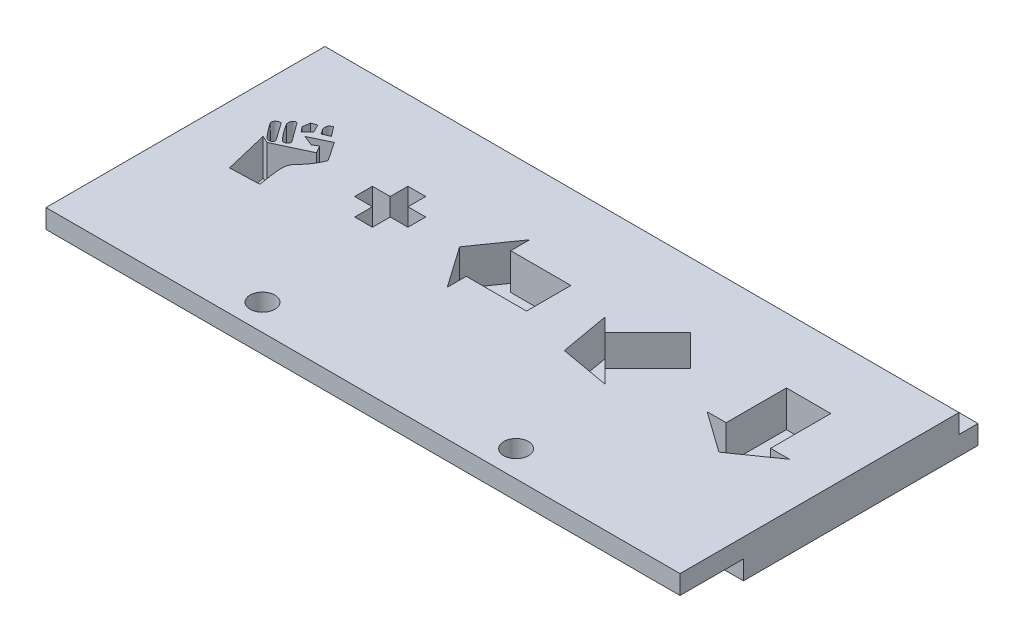
SolidWorks part; units mm, degrees
ref_plane "Front Plane" through (0, 0, 0) normal (0, 0, 1) x (1, 0, 0)
ref_plane "Top Plane" through (0, 0, 0) normal (0, 1, 0) x (1, 0, 0)
ref_plane "Right Plane" through (0, 0, 0) normal (1, 0, 0) x (0, 0, -1)
sketch "Sketch1" plane through (0, 0, 0) normal (0, 1, 0) x (1, 0, 0)
  line L1 (0, 0) -> (100, 0)
  line L2 (0, 0) -> (0, 50)
  line L3 (0, 50) -> (100, 50)
  line L4 (100, 0) -> (100, 50)
  dimension "D1" = 50
  dimension "D2" = 100
extrude "Boss-Extrude1" add sketch "Sketch1" along normal blind 6
sketch "Sketch2" plane through (100, 0, 0) normal (1, 0, 0) x (0, 0, -1)
  line L1 (0, 0) -> (10, 0)
  line L2 (0, 0) -> (0, 3)
  line L3 (0, 3) -> (10, 3)
  line L4 (10, 0) -> (10, 3)
  dimension "D1" = 10
  dimension "D2" = 3
extrude "Cut-Extrude1" cut sketch "Sketch2" against normal through all
sketch "Sketch3" plane through (100, 0, 0) normal (1, 0, 0) x (0, 0, -1)
  line L1 (50, 0) -> (44, 0)
  line L2 (50, 0) -> (50, 34)
  line L3 (50, 34) -> (44, 34)
  line L4 (44, 0) -> (44, 34)
  dimension "D1" = 6
  dimension "D2" = 34
extrude "Boss-Extrude2" add sketch "Sketch3" against normal up to surface (100 mm away) up to face at (0, 3, -20)
sketch "Sketch4" plane through (0, 0, 0) normal (-1, 0, 0) x (0, 0, 1)
  line L1 (-44, 34) -> (-46, 34)
  line L2 (-44, 34) -> (-44, 31)
  line L3 (-44, 31) -> (-46, 31)
  line L4 (-46, 34) -> (-46, 31)
  dimension "D1" = 2
  dimension "D2" = 3
extrude "Cut-Extrude2" cut sketch "Sketch4" against normal through all
sketch "Sketch5" plane through (0, 0, -44) normal (0, 0, -1) x (-1, 0, 0)
  line L0 (-7, 25) -> (-95, 25) construction
  line L1 (-45.0882, 17.5714) -> (-45.4397, 17.4542)
  line L2 (0, 34) -> (-100, 34) construction
  line L5 (-17.0385, 9.6194) -> (-19.4883, 12.0859)
  line L6 (-19.4883, 12.0859) -> (-19.5357, 12.3092)
  line L7 (-19.5357, 12.3092) -> (-19.5273, 14.7589)
  line L8 (-19.5273, 14.7589) -> (-19.4855, 14.904)
  line L9 (-19.4855, 14.904) -> (-16.8962, 17.4542)
  line L10 (-16.8962, 17.4542) -> (-16.5558, 17.5714)
  line L11 (-16.5558, 17.5714) -> (-10.25, 17.5714)
  line L12 (-10.25, 17.5714) -> (-10.2444, 23.8689)
  line L13 (-8.8214, 23.7405) -> (-8.8214, 9.8008)
  line L15 (-9.7478, 9.3767) -> (-16.3744, 9.3571)
  line L16 (-18.1071, 12.5631) -> (-16.154, 10.6071)
  line L17 (-16.154, 10.6071) -> (-10.25, 10.6071)
  line L18 (-10.25, 10.6071) -> (-10.25, 16.3214)
  line L19 (-10.25, 16.3214) -> (-16.1373, 16.3214)
  line L20 (-16.1373, 16.3214) -> (-18.1071, 14.3683)
  line L21 (-18.1071, 14.3683) -> (-18.1071, 12.5631)
  line L23 (-33.8214, 10.1328) -> (-33.8158, 23.88)
  line L25 (-33.1406, 24.3571) -> (-23.5089, 24.3571)
  line L27 (-23.1071, 23.5229) -> (-23.1071, 9.7812)
  line L28 (-23.6094, 9.3571) -> (-33.2355, 9.3795)
  line L29 (-32.3929, 23.1071) -> (-32.3929, 10.6071)
  line L30 (-32.3929, 10.6071) -> (-24.5357, 10.6071)
  line L31 (-24.5357, 10.6071) -> (-24.5357, 23.1071)
  line L32 (-24.5357, 23.1071) -> (-32.3929, 23.1071)
  line L33 (-45.6099, 9.6194) -> (-48.0597, 12.0859)
  line L34 (-48.0597, 12.0859) -> (-48.1071, 12.3092)
  line L35 (-48.1071, 12.3092) -> (-48.0988, 14.7617)
  line L36 (-48.0988, 14.7617) -> (-48.0569, 14.9012)
  line L37 (-48.0569, 14.9012) -> (-45.4397, 17.4542)
  line L39 (-45.0882, 17.5714) -> (-41.6814, 17.5714)
  line L40 (-41.6814, 17.5714) -> (-48.0318, 23.5731)
  line L41 (-46.9911, 24.2595) -> (-40.1161, 17.5714)
  line L42 (-40.1161, 17.5714) -> (-38.8214, 17.5714)
  line L43 (-38.8214, 17.5714) -> (-38.8186, 23.88)
  line L44 (-37.3929, 23.7405) -> (-37.3929, 9.8008)
  line L46 (-38.3192, 9.3767) -> (-44.9459, 9.3571)
  line L47 (-46.6786, 12.5575) -> (-44.7254, 10.6071)
  line L48 (-44.7254, 10.6071) -> (-38.8214, 10.6071)
  line L49 (-38.8214, 10.6071) -> (-38.8214, 16.3214)
  line L50 (-38.8214, 16.3214) -> (-44.7087, 16.3214)
  line L51 (-44.7087, 16.3214) -> (-46.6786, 14.3544)
  line L52 (-46.6786, 14.3544) -> (-46.6786, 12.5575)
  line L54 (-62.3929, 10.1328) -> (-62.3873, 23.88)
  line L56 (-61.7121, 24.3571) -> (-52.0804, 24.3571)
  line L58 (-51.6786, 23.5229) -> (-51.6786, 9.7812)
  line L59 (-52.1808, 9.3571) -> (-61.8069, 9.3795)
  line L60 (-60.9643, 23.1071) -> (-60.9643, 10.6071)
  line L61 (-60.9643, 10.6071) -> (-53.1071, 10.6071)
  line L62 (-53.1071, 10.6071) -> (-53.1071, 23.1071)
  line L63 (-53.1071, 23.1071) -> (-60.9643, 23.1071)
  line L65 (-76.5167, 10.2249) -> (-69.8343, 16.8906)
  line L66 (-69.8343, 16.8906) -> (-76.5084, 23.5647)
  line L67 (-75.4565, 24.2595) -> (-68.6708, 17.5714)
  line L68 (-68.6708, 17.5714) -> (-67.3929, 17.5714)
  line L69 (-67.3929, 17.5714) -> (-67.3901, 23.88)
  line L70 (-65.9643, 23.7405) -> (-65.9643, 9.7896)
  line L71 (-67.3929, 10.1384) -> (-67.3929, 16.3214)
  line L72 (-67.3929, 16.3214) -> (-68.668, 16.3214)
  line L73 (-68.668, 16.3214) -> (-75.49, 9.466)
  line L74 (-81.6786, 10.13) -> (-81.6786, 21.2266)
  line L75 (-81.6786, 21.2266) -> (-83.5703, 23.1071)
  line L76 (-83.5703, 23.1071) -> (-87.5854, 23.1071)
  line L77 (-87.5854, 23.1071) -> (-89.5357, 21.1512)
  line L78 (-89.5357, 21.1512) -> (-89.5357, 9.7701)
  line L79 (-90.9643, 10.1356) -> (-90.8834, 21.7511)
  line L80 (-90.8834, 21.7511) -> (-88.2578, 24.3209)
  line L81 (-88.2578, 24.3209) -> (-87.8728, 24.3571)
  line L82 (-87.8728, 24.3571) -> (-82.9704, 24.3571)
  line L83 (-82.9704, 24.3571) -> (-82.7891, 24.2344)
  line L84 (-82.7891, 24.2344) -> (-80.303, 21.7427)
  line L85 (-80.303, 21.7427) -> (-80.25, 21.4805)
  line L86 (-80.25, 21.4805) -> (-80.25, 9.7812)
  arc A0 (-10.2444, 23.8689) -> (-8.8214, 23.7405) centre (-9.5272, 23.8682) cw
  arc A1 (-23.6094, 9.3571) -> (-23.1071, 9.7812) centre (-23.6082, 9.8652) ccw
  arc A2 (-33.8214, 10.1328) -> (-33.2355, 9.3795) centre (-33.0446, 10.1325) ccw
  arc A3 (-33.8158, 23.88) -> (-33.1406, 24.3571) centre (-33.3095, 23.8798) cw
  arc A4 (-23.1071, 23.5229) -> (-23.5089, 24.3571) centre (-24.1742, 23.5229) ccw
  arc A5 (-9.7478, 9.3767) -> (-8.8214, 9.8008) centre (-9.7514, 10.6083) ccw
  arc A6 (-16.3744, 9.3571) -> (-17.0385, 9.6194) centre (-16.3773, 10.3218) cw
  arc A7 (-38.3192, 9.3767) -> (-37.3929, 9.8008) centre (-38.3228, 10.6083) ccw
  arc A8 (-44.9459, 9.3571) -> (-45.6099, 9.6194) centre (-44.9487, 10.3218) cw
  arc A9 (-38.8186, 23.88) -> (-37.3929, 23.7405) centre (-38.8219, 16.4911) cw
  arc A10 (-46.9911, 24.2595) -> (-48.0318, 23.5731) centre (-47.4361, 23.802) ccw
  arc A11 (-52.1808, 9.3571) -> (-51.6786, 9.7812) centre (-52.1796, 9.8652) ccw
  arc A12 (-61.8069, 9.3795) -> (-62.3929, 10.1328) centre (-61.8055, 9.9851) cw
  arc A13 (-62.3873, 23.88) -> (-61.7121, 24.3571) centre (-61.881, 23.8798) cw
  arc A14 (-51.6786, 23.5229) -> (-52.0804, 24.3571) centre (-52.7456, 23.5229) ccw
  arc A15 (-67.3929, 10.1384) -> (-65.9643, 9.7896) centre (-66.636, 10.1384) ccw
  arc A16 (-76.5167, 10.2249) -> (-75.49, 9.466) centre (-73.495, 13.239) ccw
  arc A17 (-65.9643, 23.7405) -> (-67.3901, 23.88) centre (-66.684, 23.7405) ccw
  arc A18 (-75.4565, 24.2595) -> (-76.5084, 23.5647) centre (-75.9088, 23.8006) ccw
  arc A19 (-80.25, 9.7812) -> (-81.6786, 10.13) centre (-80.25, 12.8814) cw
  arc A20 (-89.5357, 9.7701) -> (-90.9643, 10.1356) centre (-89.5357, 12.7446) cw
  dimension "D1" = 9
extrude "Cut-Extrude3" cut sketch "Sketch5" along normal blind 5.5
sketch "Sketch8" plane through (0, 6, 0) normal (0, 1, 0) x (1, 0, 0)
  line L0 (46.515, 10) -> (46.515, 44) construction
  line L1 (60.1307, 150.748) -> (217.464, 150.748) construction
  line L2 (130, 309) -> (530, 309) construction
  line L3 (101.6667, 132) -> (448.3333, 132) construction
  line L4 (92.1667, 73.5) -> (454.8333, 73.5) construction
  line L12 (92.1667, 73.5) -> (454.8333, 73.5) construction
  line L30 (100, 44) -> (0, 44) construction
  line L64 (50, 44) -> (50, 5.4119) construction
  line L65 (7.0116, 30.0772) -> (8.9551, 27.3326)
  line L66 (8.4762, 31.0134) -> (10.3204, 28.5061)
  line L67 (10.8168, 31.4007) -> (10.155, 32.7243)
  line L68 (9.8241, 30.4081) -> (10.8168, 31.4007)
  line L69 (9.1624, 31.2353) -> (9.8241, 30.4081)
  line L70 (9.3278, 32.3934) -> (9.1624, 31.2353)
  line L71 (10.155, 32.7243) -> (9.3278, 32.3934)
  line L72 (12.8021, 32.2279) -> (11.644, 33.7169)
  line L73 (11.644, 31.7316) -> (12.8021, 32.2279)
  line L74 (11.644, 31.7316) -> (11.0923, 32.5507)
  line L75 (13.193, 29.9735) -> (13.8548, 28.8154)
  line L76 (13.8548, 28.8154) -> (8.5607, 26.3338)
  line L77 (8.5607, 26.3338) -> (7.4026, 26.8301)
  line L78 (7.4026, 26.8301) -> (9.057, 19.8816)
  line L79 (9.057, 19.8816) -> (13.6893, 20.0471)
  line L80 (15.8401, 28.65) -> (13.8548, 31.6279)
  line L81 (13.8548, 31.6279) -> (10.7114, 30.139)
  line L82 (10.7114, 30.139) -> (12.3658, 29.4772)
  line L83 (13.193, 29.9735) -> (12.3658, 29.4772)
  line L84 (31.2401, 25.85) -> (31.2401, 28.65)
  line L85 (28.4401, 25.85) -> (31.2401, 25.85)
  line L86 (28.4401, 23.05) -> (28.4401, 25.85)
  line L87 (25.6401, 23.05) -> (28.4401, 23.05)
  line L88 (25.6401, 25.85) -> (25.6401, 23.05)
  line L89 (22.8401, 25.85) -> (25.6401, 25.85)
  line L90 (22.8401, 28.65) -> (22.8401, 25.85)
  line L91 (25.6401, 28.65) -> (22.8401, 28.65)
  line L92 (25.6401, 31.45) -> (25.6401, 28.65)
  line L93 (28.4401, 31.45) -> (25.6401, 31.45)
  line L94 (28.4401, 28.65) -> (28.4401, 31.45)
  line L95 (31.2401, 28.65) -> (28.4401, 28.65)
  line L96 (52.0414, 30.75) -> (42.5414, 30.75)
  line L97 (52.0414, 30.75) -> (52.0414, 23.75)
  line L98 (52.0414, 23.75) -> (42.5414, 23.75)
  line L99 (42.5414, 20.75) -> (42.5414, 23.75)
  line L100 (37.9901, 27.25) -> (42.5414, 20.75)
  line L101 (42.5414, 33.75) -> (37.9901, 27.25)
  line L102 (42.5414, 30.75) -> (42.5414, 33.75)
  line L103 (60.4193, 21.3393) -> (59.0414, 29.1538)
  line L104 (68.2338, 19.9614) -> (60.4193, 21.3393)
  line L105 (66.1125, 22.0827) -> (68.2338, 19.9614)
  line L106 (72.83, 28.8003) -> (66.1125, 22.0827)
  line L107 (67.8803, 33.75) -> (72.83, 28.8003)
  line L108 (61.1627, 27.0325) -> (67.8803, 33.75)
  line L109 (59.0414, 29.1538) -> (61.1627, 27.0325)
  line L110 (90.03, 33.75) -> (90.03, 24.25)
  line L111 (90.03, 33.75) -> (83.03, 33.75)
  line L112 (83.03, 33.75) -> (83.03, 24.25)
  line L113 (80.03, 24.25) -> (83.03, 24.25)
  line L114 (86.4768, 19.6614) -> (80.03, 24.25)
  line L115 (93.03, 24.25) -> (86.4768, 19.6614)
  line L116 (90.03, 24.25) -> (93.03, 24.25)
  spline S9 degree 2 poles (7.8995, 26.9338) (6.9675, 27.996) (6.1739, 29.1623) knots 0 0 0 1 1 1
  spline S10 degree 3 poles (8.9551, 27.3326) (9.1296, 26.7307) (8.2077, 26.5734) (7.8995, 26.9338) knots 0 0 0 0 1 1 1 1
  spline S11 degree 3 poles (6.1739, 29.1623) (5.8271, 29.6649) (6.5306, 30.2426) (7.0116, 30.0772) knots 0 0 0 0 1 1 1 1
  spline S12 degree 3 poles (7.5484, 30.4081) (7.4209, 30.7808) (7.6573, 31.5729) (8.1697, 31.4007) knots 0 0 0 0 1 1 1 1
  spline S13 degree 2 poles (7.5484, 30.4081) (8.3692, 29.0037) (9.4644, 27.8067) knots 0 0 0 1 1 1
  spline S14 degree 3 poles (10.3204, 28.5061) (10.7529, 28.0224) (9.8445, 27.3259) (9.4644, 27.8067) knots 0 0 0 0 1 1 1 1
  spline S15 degree 2 poles (8.1697, 31.4007) (8.3652, 31.2409) (8.4762, 31.0134) knots 0 0 0 1 1 1
  spline S16 degree 2 poles (11.644, 33.7169) (10.8014, 33.411) (11.0923, 32.5507) knots 0 0 0 1 1 1
  spline S17 degree 3 poles (13.6893, 20.0471) (12.4502, 27.1719) (13.7772, 23.8367) (15.8401, 28.65) knots 0 0 0 0 1 1 1 1
extrude "Cut-Extrude4" cut sketch "Sketch8" against normal blind 5.7
sketch "Sketch9" plane through (0, 0, 0) normal (-1, 0, 0) x (0, 0, 1)
  line L0 (-50, 6) -> (-50, 0)
  line L1 (-50, 34) -> (-44, 34)
  line L2 (-50, 34) -> (-50, 6)
  line L4 (-44, 34) -> (-44, 6)
  line L5 (-50, 0) -> (-47, 0)
  line L6 (-50, 0) -> (-10, 0) construction
  line L7 (-47, 0) -> (-47, 3)
  line L8 (-47, 3) -> (-44, 3)
  line L9 (-44, 3) -> (-44, 6)
  dimension "D1" = 3
  dimension "D2" = 3
extrude "Cut-Extrude5" cut sketch "Sketch9" against normal through all
sketch "Sketch10" plane through (0, 6, 0) normal (0, 1, 0) x (1, 0, 0)
  circle A0 centre (70, 4.1444) radius 1.95
  dimension "D1" = 3.9
extrude "Cut-Extrude6" cut sketch "Sketch10" against normal through all
sketch "Sketch11" plane through (0, 6, 0) normal (0, 1, 0) x (1, 0, 0)
  circle A0 centre (30, 4.1444) radius 1.95
  dimension "D1" = 3.9
extrude "Cut-Extrude7" cut sketch "Sketch11" against normal through all
